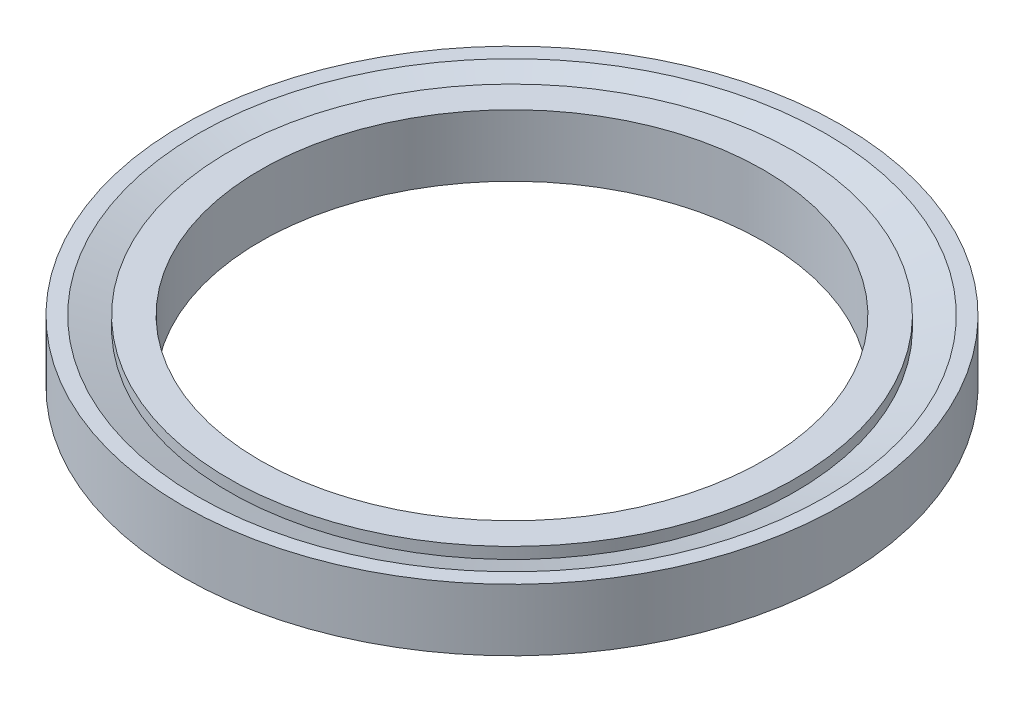
SolidWorks part; units mm, degrees
material "Copper"
ref_plane "Front Plane" through (0, 0, 0) normal (0, 0, 1) x (1, 0, 0)
ref_plane "Top Plane" through (0, 0, 0) normal (0, 1, 0) x (1, 0, 0)
ref_plane "Right Plane" through (0, 0, 0) normal (1, 0, 0) x (0, 0, -1)
sketch "Sketch1" plane through (0, 0, 0) normal (0, 0, 1) x (1, 0, 0)
  line L0 (0, 1) -> (0, -1) construction
  line L2 (0, 1) -> (10.6426, 1)
  line L3 (0, 1) -> (0, -1)
  line L4 (0, -1) -> (10.6426, -1)
  line L5 (10.6426, 1) -> (10.6426, -1)
  dimension "D3" = 2
  dimension "OD" = 21.2852
revolve "Revolve1" add sketch "Sketch1" angle 360 about L0
sketch "Sketch2" plane through (0, 0, 0) normal (0, 0, 1) x (1, 0, 0)
  line L0 (-9.144, 0.635) -> (-9.144, 1.2174)
  line L1 (-9.144, 1.2174) -> (-10.7442, 1.2174)
  line L2 (-10.7442, 1.2174) -> (-9.144, 0.635)
  line L4 (0, 0) -> (0, 2.4004) construction
  line L5 (0, 0) -> (-11.7103, 0) construction
  line L6 (-10.7442, -1.2174) -> (-9.144, -0.635)
  line L7 (-9.144, -1.2174) -> (-10.7442, -1.2174)
  line L8 (-9.144, -0.635) -> (-9.144, -1.2174)
  dimension "D1" = 20
  dimension "D2" = 0.635
  dimension "Knife Length" = 1.6002
  dimension "Flange ID" = 10.7442
revolve "Cut-Revolve1" cut sketch "Sketch2" angle 360 about L4
sketch "Sketch3" plane through (0, 1, 0) normal (0, 1, 0) x (1, 0, 0)
  circle A0 centre (0, 0) radius 8.128
  dimension "ID" = 16.256
extrude "Cut-Extrude1" cut sketch "Sketch3" against normal through all
